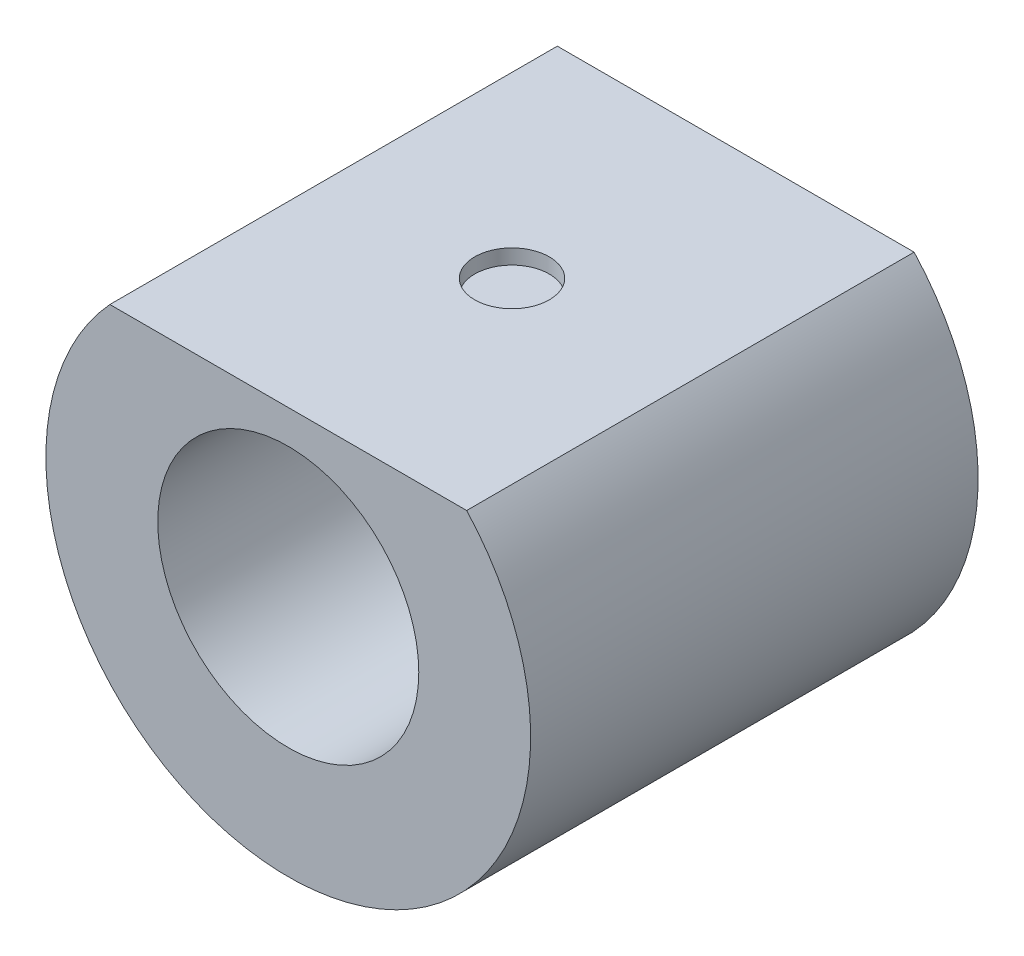
SolidWorks part; units mm, degrees
ref_plane "Front Plane" through (0, 0, 0) normal (0, 0, 1) x (1, 0, 0)
ref_plane "Top Plane" through (0, 0, 0) normal (0, 1, 0) x (1, 0, 0)
ref_plane "Right Plane" through (0, 0, 0) normal (1, 0, 0) x (0, 0, -1)
sketch "Sketch1" plane through (0, 0, 0) normal (0, 0, 1) x (1, 0, 0)
  circle A0 centre (0, 0) radius 32.5
  dimension "D1" = 65
extrude "Boss-Extrude1" add sketch "Sketch1" along normal blind 60
sketch "Sketch3" plane through (0, 0, 60) normal (0, 0, 1) x (1, 0, 0)
  circle A0 centre (0, 0) radius 17.5
  dimension "D1" = 35
extrude "Cut-Extrude4" cut sketch "Sketch3" against normal blind 52
sketch "Sketch6" plane through (0, 0, 8) normal (0, 0, 1) x (1, 0, 0)
  circle A0 centre (0, 0) radius 6.5
  dimension "D1" = 13
extrude "Cut-Extrude5" cut sketch "Sketch6" against normal blind 8
sketch "Sketch8" plane through (0, 0, 60) normal (0, 0, 1) x (1, 0, 0)
  line L0 (0, 32.5) -> (-41.4519, 32.5) construction
  line L1 (0, 22) -> (-42.4191, 22) construction
  line L3 (-33.9906, 33.9215) -> (31.3653, 33.9215)
  line L4 (-33.9906, 33.9215) -> (-33.9906, 22)
  line L5 (-33.9906, 22) -> (31.3653, 22)
  line L6 (31.3653, 33.9215) -> (31.3653, 22)
  circle A0 centre (0, 0) radius 32.5 construction
  dimension "D1" = 10.5
extrude "Cut-Extrude6" cut sketch "Sketch8" against normal blind 60
sketch "Sketch9" plane through (0, 22, 0) normal (0, 1, 0) x (1, 0, 0)
  line L0 (0, 0) -> (0, -53.534) construction
  line L1 (-23.9217, 0) -> (23.9217, 0) construction
  line L2 (23.9217, -30) -> (-23.9217, -30) construction
  line L3 (23.9217, 0) -> (23.9217, -60) construction
  line L4 (-23.9217, -60) -> (-23.9217, 0) construction
  circle A0 centre (0, -30) radius 5
  dimension "D1" = 10
extrude "Cut-Extrude9" cut sketch "Sketch9" against normal blind 2
